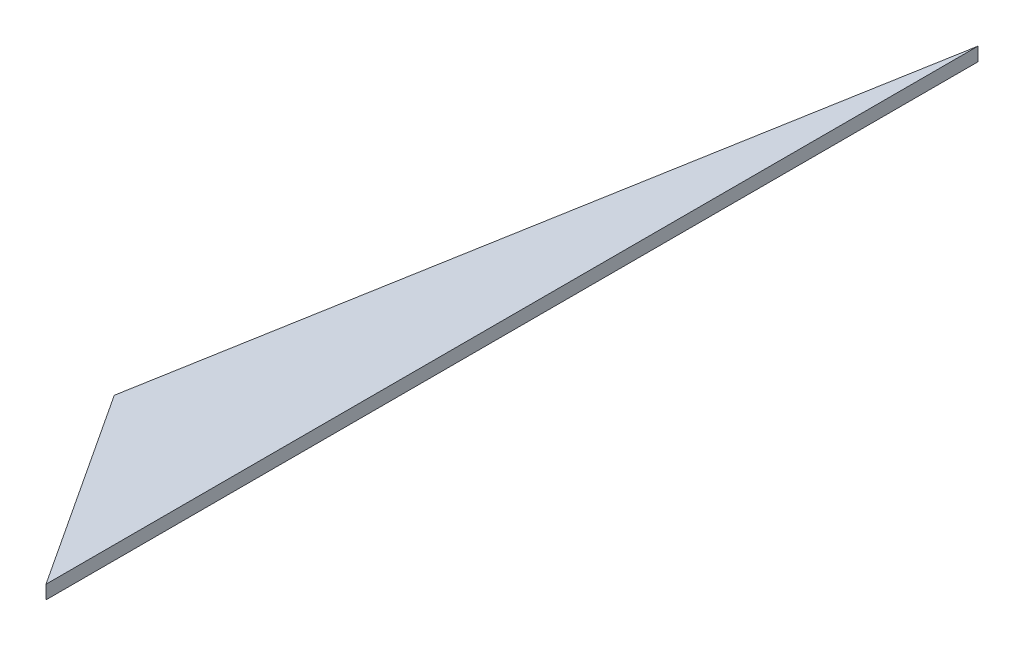
SolidWorks part; units mm, degrees
ref_plane "Front Plane" through (0, 0, 0) normal (0, 0, 1) x (1, 0, 0)
ref_plane "Top Plane" through (0, 0, 0) normal (0, 1, 0) x (1, 0, 0)
ref_plane "Right Plane" through (0, 0, 0) normal (1, 0, 0) x (0, 0, -1)
sketch "Sketch1" plane through (0, 0, 0) normal (0, 1, 0) x (1, 0, 0)
  line L0 (0, 0) -> (0, 6096)
  line L1 (0, 6096) -> (-846.8474, 1293.2896)
  line L2 (-846.8474, 1293.2896) -> (0, 0)
  line L4 (0, 0) -> (-1219.2, 0) construction
  line L5 (0, 0) -> (0, 6096) construction
  line L6 (0, 6096) -> (-1219.2, 6096) construction
  line L7 (-1219.2, 0) -> (-1219.2, 6096) construction
  point P3 (94.1235, 0)
  point P5 (-2688.3237, 0)
  point P6 (-1513.8233, 6096)
  point P7 (-1863.377, 5657.9434)
  point P11 (0, 5909.6221)
  dimension "D1" = 6096
  dimension "D2" = 4876.8
  dimension "D3" = 10
  dimension "D4" = 1219.2
extrude "Boss-Extrude1" add sketch "Sketch1" along normal blind 88.9
